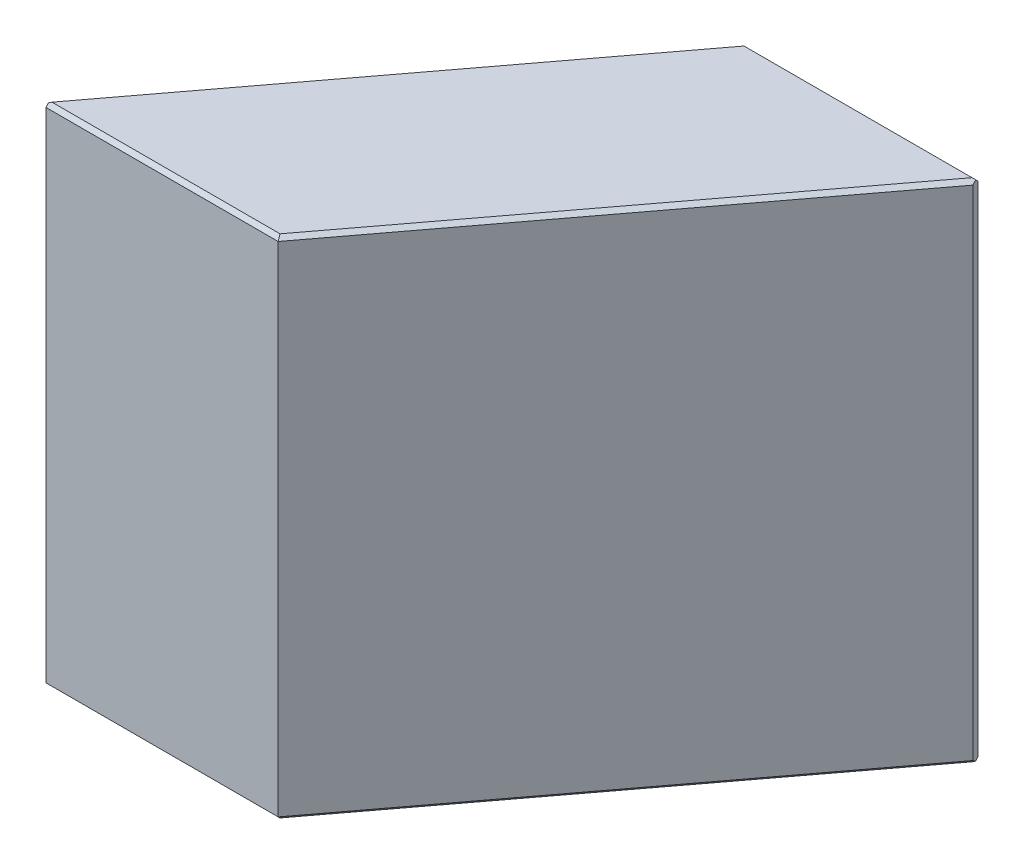
SolidWorks part; units mm, degrees
material "Стекло"
ref_plane "Спереди" through (0, 0, 0) normal (0, 0, 1) x (1, 0, 0)
ref_plane "Сверху" through (0, 0, 0) normal (0, 1, 0) x (1, 0, 0)
ref_plane "Справа" through (0, 0, 0) normal (1, 0, 0) x (0, 0, -1)
sketch "Эскиз1" plane through (0, 0, 0) normal (0, 1, 0) x (1, 0, 0)
  line L0 (11.9815, 15.9) -> (21.3725, 15.9)
  line L1 (0, 0) -> (9.391, 0)
  line L2 (5.4986, -29.6) -> (5.4986, 26.0716) construction
  line L3 (0, 0) -> (11.9815, 15.9)
  line L4 (9.391, 0) -> (21.3725, 15.9)
  dimension "D1" = 15.9
  dimension "D2" = 7.5
  dimension "D3" = 53
extrude "Вытянуть1" add sketch "Эскиз1" along normal blind 20
chamfer "Фаска1" distance 0.15 angle 45 10 edges at (16.677, 0, -15.9) (5.9908, 0, -7.95) (4.6955, 0, 0) (15.3818, 0, -7.95) (4.6955, 20, 0) (15.3818, 20, -7.95) (5.9908, 20, -7.95) (16.677, 20, -15.9) (0, 10, 0) (21.3725, 10, -15.9)
chamfer "Фаска2" distance 0.3 angle 45 2 edges at (0, 10, 0) (21.3725, 10, -15.9)
